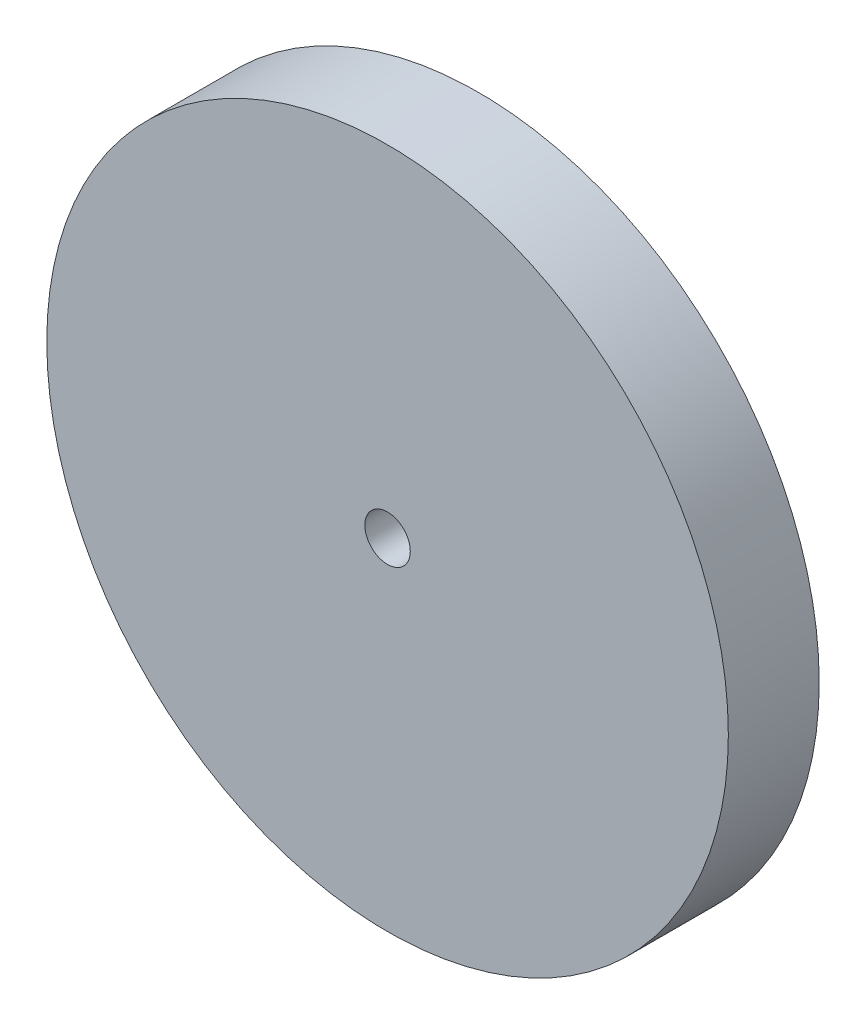
SolidWorks part; units mm, degrees
material "ABS"
ref_plane "前视基准面" through (0, 0, 0) normal (0, 0, 1) x (1, 0, 0)
ref_plane "上视基准面" through (0, 0, 0) normal (0, 1, 0) x (1, 0, 0)
ref_plane "右视基准面" through (0, 0, 0) normal (1, 0, 0) x (0, 0, -1)
other "Configuration Table"
sketch "草图1" plane through (0, 0, 0) normal (0, 0, 1) x (1, 0, 0)
  circle A0 centre (0, 0) radius 15
  dimension "D1" = 30
extrude "凸台-拉伸1" add sketch "草图1" along normal blind 4
sketch "草图2" plane through (0, 0, 4) normal (0, 0, 1) x (1, 0, 0)
  circle A0 centre (0, 0) radius 1
  dimension "D1" = 2
extrude "切除-拉伸1" cut sketch "草图2" against normal through all
